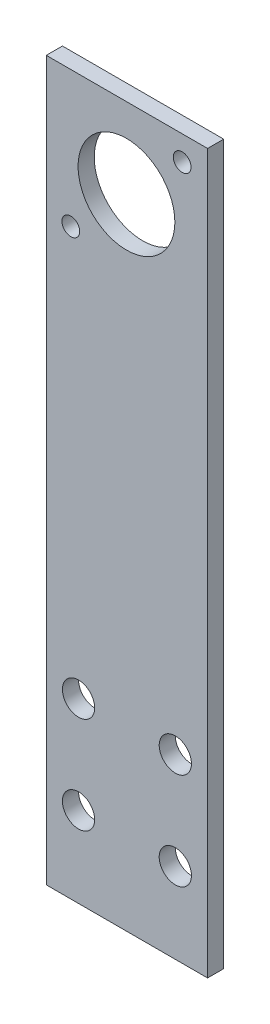
SolidWorks part; units mm, degrees
ref_plane "Front Plane" through (0, 0, 0) normal (0, 0, 1) x (1, 0, 0)
ref_plane "Top Plane" through (0, 0, 0) normal (0, 1, 0) x (1, 0, 0)
ref_plane "Right Plane" through (0, 0, 0) normal (1, 0, 0) x (0, 0, -1)
sketch "Sketch1" plane through (0, 0, 0) normal (0, 0, 1) x (1, 0, 0)
  line L1 (0, 0) -> (31.75, 0)
  line L2 (0, 0) -> (0, 147.32)
  line L3 (0, 147.32) -> (31.75, 147.32)
  line L4 (31.75, 0) -> (31.75, 147.32)
  dimension "D1" = 147.32
  dimension "D2" = 31.75
extrude "Boss-Extrude1" add sketch "Sketch1" along normal blind 3.175
sketch "Sketch2" plane through (0, 0, 3.175) normal (0, 0, 1) x (1, 0, 0)
  line L0 (31.75, 147.32) -> (0, 147.32) construction
  line L1 (0, 147.32) -> (0, 0) construction
  line L3 (31.75, 0) -> (31.75, 147.32) construction
  circle A0 centre (4.826, 142.494) radius 1.778
  circle A2 centre (26.924, 120.396) radius 1.778
  circle A3 centre (15.875, 131.318) radius 10.16
  dimension "D2" = 3.556
  dimension "D4" = 4.826
  dimension "D5" = 26.924
  dimension "D6" = 16.002
  dimension "D7" = 15.875
  dimension "D1" = 4.826
  dimension "D3" = 4.826
extrude "Cut-Extrude2" [suppressed] cut sketch "Sketch2" against normal up to next
sketch "Sketch5" plane through (0, 0, 3.175) normal (0, 0, 1) x (1, 0, 0)
  line L0 (31.75, 0) -> (31.75, 147.32) construction
  line L1 (0, 0) -> (31.75, 0)
  line L2 (0, 0) -> (0, 5.842)
  line L3 (0, 5.842) -> (31.75, 5.842)
  line L4 (31.75, 0) -> (31.75, 5.842)
extrude "Cut-Extrude4" cut sketch "Sketch5" against normal up to next
sketch "Sketch6" plane through (0, 0, 3.175) normal (0, 0, 1) x (1, 0, 0)
  line L0 (31.75, 5.842) -> (31.75, 147.32) construction
  line L1 (0, 5.842) -> (31.75, 5.842)
  line L2 (0, 5.842) -> (0, 5.9055)
  line L3 (0, 5.9055) -> (31.75, 5.9055)
  line L4 (31.75, 5.842) -> (31.75, 5.9055)
  dimension "D1" = 0.0635
extrude "Cut-Extrude5" cut sketch "Sketch6" against normal up to next
ref_plane "Plane1" through (0, 5.9055, 0) normal (0, 0, 1) x (1, 0, 0)
sketch "Sketch8" plane through (0, 0, 3.175) normal (0, 0, 1) x (1, 0, 0)
  line L0 (6.35, 21.7805) -> (25.4, 21.7805) construction
  line L1 (6.35, 21.7805) -> (6.35, 40.8305) construction
  line L2 (6.35, 40.8305) -> (25.4, 40.8305) construction
  line L3 (25.4, 21.7805) -> (25.4, 40.8305) construction
  line L4 (6.35, 21.7805) -> (25.4, 40.8305) construction
  line L5 (6.35, 40.8305) -> (25.4, 21.7805) construction
  line L6 (35.186, 31.3055) -> (3.436, 31.3055) construction
  line L7 (15.875, 147.32) -> (15.875, 5.9055) construction
  line L8 (31.75, 147.32) -> (0, 147.32) construction
  line L9 (31.75, 5.9055) -> (0, 5.9055) construction
  circle A0 centre (25.4, 40.8305) radius 3.175
  circle A1 centre (6.35, 40.8305) radius 3.175
  circle A2 centre (6.35, 21.7805) radius 3.175
  circle A3 centre (25.4, 21.7805) radius 3.175
  point P2 (15.875, 31.3055)
  point P17 (15.875, 25.634)
  point P18 (15.875, 31.3055)
  dimension "D2" = 6.35
  dimension "D1" = 19.05
  dimension "D3" = 25.4
extrude "Cut-Extrude6" cut sketch "Sketch8" against normal up to next
sketch "Sketch10" plane through (0, 0, 3.175) normal (0, 0, 1) x (1, 0, 0)
  line L0 (4.826, 120.5738) -> (26.7462, 142.494) construction
  arc A4 (6.5786, 120.5738) -> (3.0734, 120.5738) centre (4.826, 120.5738) ccw
  arc A5 (3.0734, 120.5738) -> (6.5786, 120.5738) centre (4.826, 120.5738) ccw
  arc A6 (24.9936, 142.494) -> (28.4988, 142.494) centre (26.7462, 142.494) ccw
  arc A7 (28.4988, 142.494) -> (24.9936, 142.494) centre (26.7462, 142.494) ccw
  circle A8 centre (15.7861, 131.5339) radius 9.525
  dimension "D1" = 19.05
extrude "Cut-Extrude7" cut sketch "Sketch10" against normal through all
